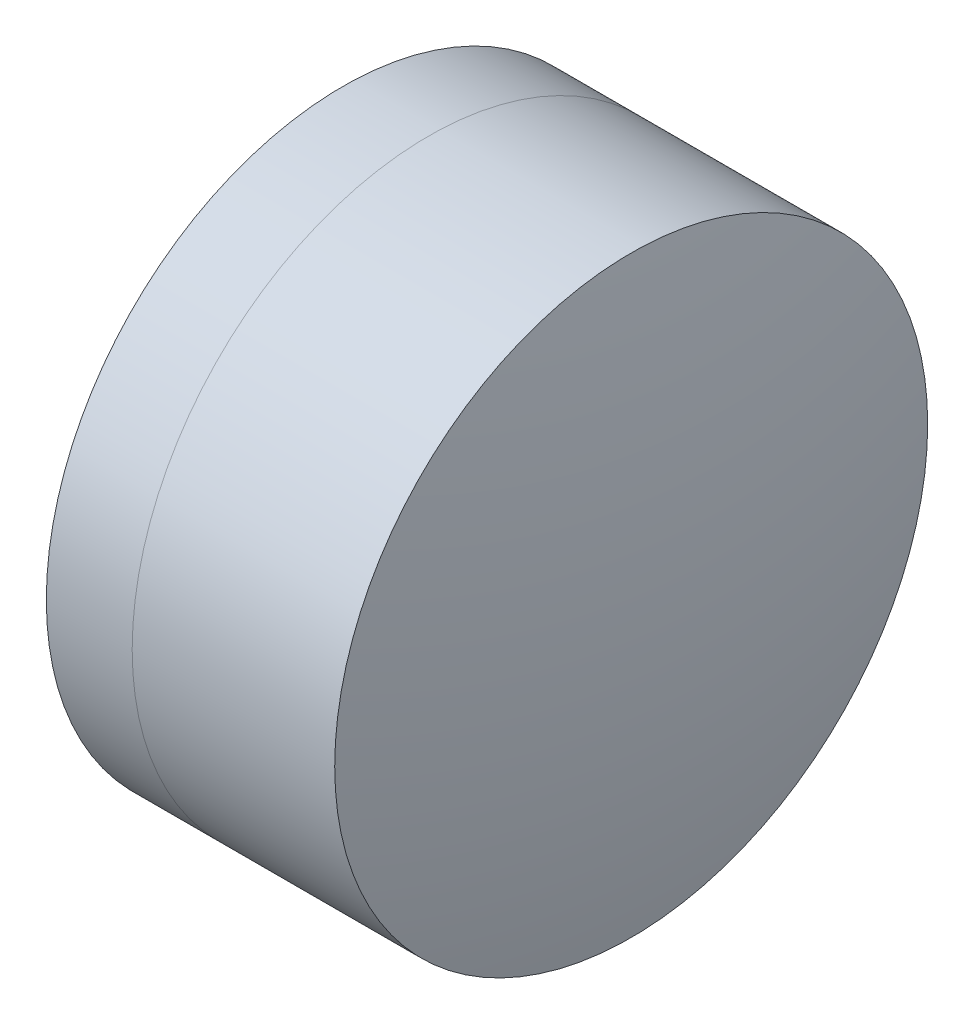
SolidWorks part; units mm, degrees
ref_plane "前视基准面" through (0, 0, 0) normal (0, 0, 1) x (1, 0, 0)
ref_plane "上视基准面" through (0, 0, 0) normal (0, 1, 0) x (1, 0, 0)
ref_plane "右视基准面" through (0, 0, 0) normal (1, 0, 0) x (0, 0, -1)
sketch "草图1" plane through (0, 0, 0) normal (0, 1, 0) x (1, 0, 0)
  line L0 (-9.7026, 0) -> (11.7646, 0) construction
  line L1 (-1.9628, -4) -> (-0.8044, -4)
  line L2 (-1.9628, 4) -> (-0.8044, 4)
  arc A0 (-0.8044, -4) -> (-0.8044, 4) centre (-6.6292, 0) ccw
  arc A1 (-1.9628, 4) -> (-1.9628, -4) centre (7.8988, 0) ccw
  point P10 (-2.7432, 0)
  point P11 (0.4368, 0)
  dimension "D3" = 10.642
  dimension "D4" = 7.066
  dimension "D1" = 4
  dimension "D2" = 4
  dimension "D5" = 3.18
revolve "旋转1" add sketch "草图1" angle 360 about L0
sketch "草图2" plane through (0, 0, 0) normal (0, 1, 0) x (1, 0, 0)
  line L0 (-0.5519, 0) -> (13.3053, 0) construction
  line L2 (-0.8044, 4) -> (1.928, 4)
  line L3 (-0.8044, -4) -> (1.928, -4)
  arc A0 (1.928, -4) -> (1.928, 4) centre (-16.5122, 0) ccw
  arc A1 (-0.8044, -4) -> (-0.8044, 4) centre (-6.6292, 0) ccw construction
  arc A2 (-0.8044, -4) -> (-0.8044, 4) centre (-6.6292, 0) ccw
  point P4 (0.4368, 0)
  point P8 (2.3568, 0)
  dimension "D1" = 18.869
  dimension "D2" = 1.92
revolve "旋转3" add sketch "草图2" angle 360 about L0
